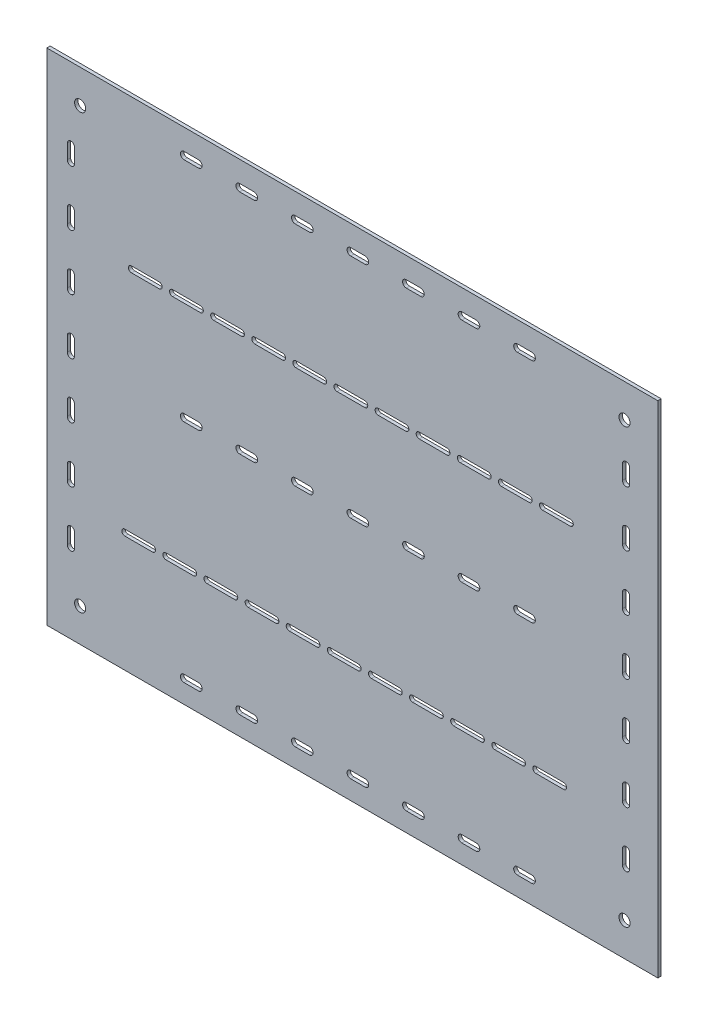
SolidWorks part; units mm, degrees
ref_plane "Alzado" through (0, 0, 0) normal (0, 0, 1) x (1, 0, 0)
ref_plane "Planta" through (0, 0, 0) normal (0, 1, 0) x (1, 0, 0)
ref_plane "Vista lateral" through (0, 0, 0) normal (1, 0, 0) x (0, 0, -1)
ref_plane "Plano1" through (0, 0, 0) normal (0, 0, -1) x (-1, 0, 0)
sketch "Croquis1" plane through (0, 0, 0) normal (0, 0, -1) x (-1, 0, 0)
  line L0 (250.0961, 147) -> (250.0961, 160)
  line L1 (256.5961, 160) -> (256.5961, 147)
  line L2 (19.8171, -120.3914) -> (-5.1829, -120.3914)
  line L3 (-5.1829, -114.9914) -> (19.8171, -114.9914)
  line L4 (-128.1829, -120.3914) -> (-153.1829, -120.3914)
  line L5 (-153.1829, -114.9914) -> (-128.1829, -114.9914)
  line L6 (93.8171, -120.3914) -> (68.8171, -120.3914)
  line L7 (68.8171, -114.9914) -> (93.8171, -114.9914)
  line L8 (-17.1829, -120.3914) -> (-42.1829, -120.3914)
  line L9 (-42.1829, -114.9914) -> (-17.1829, -114.9914)
  line L10 (167.8171, -120.3914) -> (142.8171, -120.3914)
  line L11 (142.8171, -114.9914) -> (167.8171, -114.9914)
  line L12 (56.8171, -120.3914) -> (31.8171, -120.3914)
  line L13 (31.8171, -114.9914) -> (56.8171, -114.9914)
  line L14 (179.8171, -114.9914) -> (204.8171, -114.9914)
  line L15 (204.8171, -120.3914) -> (179.8171, -120.3914)
  line L16 (105.8171, -114.9914) -> (130.8171, -114.9914)
  line L17 (130.8171, -120.3914) -> (105.8171, -120.3914)
  line L18 (-171.1819, 87.8055) -> (-196.1819, 87.8055)
  line L19 (-196.1819, 93.2055) -> (-171.1819, 93.2055)
  line L20 (-60.1819, 87.8055) -> (-85.1819, 87.8055)
  line L21 (-85.1819, 93.2055) -> (-60.1819, 93.2055)
  line L22 (51.5, -4.75) -> (38.5, -4.75)
  line L23 (38.5, 1.75) -> (51.5, 1.75)
  line L24 (151.5, -4.75) -> (138.5, -4.75)
  line L25 (138.5, 1.75) -> (151.5, 1.75)
  line L26 (13.8181, 87.8055) -> (-11.1819, 87.8055)
  line L27 (-11.1819, 93.2055) -> (13.8181, 93.2055)
  line L28 (-23.1819, 87.8055) -> (-48.1819, 87.8055)
  line L29 (-48.1819, 93.2055) -> (-23.1819, 93.2055)
  line L30 (-97.1819, 87.8055) -> (-122.1819, 87.8055)
  line L31 (-122.1819, 93.2055) -> (-97.1819, 93.2055)
  line L32 (-134.1819, 87.8055) -> (-159.1819, 87.8055)
  line L33 (-159.1819, 93.2055) -> (-134.1819, 93.2055)
  line L34 (50.8181, 87.8055) -> (25.8181, 87.8055)
  line L35 (25.8181, 93.2055) -> (50.8181, 93.2055)
  line L36 (87.8181, 87.8055) -> (62.8181, 87.8055)
  line L37 (62.8181, 93.2055) -> (87.8181, 93.2055)
  line L38 (-165.1829, -120.3914) -> (-190.1829, -120.3914)
  line L39 (-190.1829, -114.9914) -> (-165.1829, -114.9914)
  line L40 (161.8181, 87.8055) -> (136.8181, 87.8055)
  line L41 (136.8181, 93.2055) -> (161.8181, 93.2055)
  line L42 (-54.1829, -120.3914) -> (-79.1829, -120.3914)
  line L43 (-79.1829, -114.9914) -> (-54.1829, -114.9914)
  line L44 (-91.1829, -120.3914) -> (-116.1829, -120.3914)
  line L45 (-116.1829, -114.9914) -> (-91.1829, -114.9914)
  line L46 (99.8181, 93.2055) -> (124.8181, 93.2055)
  line L47 (124.8181, 87.8055) -> (99.8181, 87.8055)
  line L48 (173.8181, 93.2055) -> (198.8181, 93.2055)
  line L49 (198.8181, 87.8055) -> (173.8181, 87.8055)
  line L50 (-98.5, -4.75) -> (-111.5, -4.75)
  line L51 (-111.5, 1.75) -> (-98.5, 1.75)
  line L52 (101.5, -4.75) -> (88.5, -4.75)
  line L53 (88.5, 1.75) -> (101.5, 1.75)
  line L54 (1.5, -4.75) -> (-11.5, -4.75)
  line L55 (-11.5, 1.75) -> (1.5, 1.75)
  line L56 (-48.5, -4.75) -> (-61.5, -4.75)
  line L57 (-61.5, 1.75) -> (-48.5, 1.75)
  line L58 (151.5, -207.9595) -> (138.5, -207.9595)
  line L59 (138.5, -201.4595) -> (151.5, -201.4595)
  line L60 (-148.5, -4.75) -> (-161.5, -4.75)
  line L61 (-161.5, 1.75) -> (-148.5, 1.75)
  line L62 (101.5, -207.9595) -> (88.5, -207.9595)
  line L63 (88.5, -201.4595) -> (101.5, -201.4595)
  line L64 (51.5, -207.9595) -> (38.5, -207.9595)
  line L65 (38.5, -201.4595) -> (51.5, -201.4595)
  line L66 (101.5, 199.605) -> (88.5, 199.605)
  line L67 (88.5, 206.105) -> (101.5, 206.105)
  line L68 (-98.5, 199.605) -> (-111.5, 199.605)
  line L69 (-111.5, 206.105) -> (-98.5, 206.105)
  line L70 (151.5, 199.605) -> (138.5, 199.605)
  line L71 (138.5, 206.105) -> (151.5, 206.105)
  line L72 (51.5, 199.605) -> (38.5, 199.605)
  line L73 (38.5, 206.105) -> (51.5, 206.105)
  line L74 (1.5, -207.9595) -> (-11.5, -207.9595)
  line L75 (-11.5, -201.4595) -> (1.5, -201.4595)
  line L76 (-148.5, -207.9595) -> (-161.5, -207.9595)
  line L77 (-161.5, -201.4595) -> (-148.5, -201.4595)
  line L78 (-98.5, -207.9595) -> (-111.5, -207.9595)
  line L79 (-111.5, -201.4595) -> (-98.5, -201.4595)
  line L80 (-48.5, -207.9595) -> (-61.5, -207.9595)
  line L81 (-61.5, -201.4595) -> (-48.5, -201.4595)
  line L82 (-148.5, 199.605) -> (-161.5, 199.605)
  line L83 (-161.5, 206.105) -> (-148.5, 206.105)
  line L84 (-249.6493, -153) -> (-249.6493, -140)
  line L85 (-243.1493, -140) -> (-243.1493, -153)
  line L86 (-48.5, 199.605) -> (-61.5, 199.605)
  line L87 (-61.5, 206.105) -> (-48.5, 206.105)
  line L88 (1.5, 199.605) -> (-11.5, 199.605)
  line L89 (-11.5, 206.105) -> (1.5, 206.105)
  line L90 (-249.6493, 97) -> (-249.6493, 110)
  line L91 (-243.1493, 110) -> (-243.1493, 97)
  line L92 (-249.6493, 47) -> (-249.6493, 60)
  line L93 (-243.1493, 60) -> (-243.1493, 47)
  line L94 (-249.6493, -53) -> (-249.6493, -40)
  line L95 (-243.1493, -40) -> (-243.1493, -53)
  line L96 (-249.6493, -103) -> (-249.6493, -90)
  line L97 (-243.1493, -90) -> (-243.1493, -103)
  line L98 (250.0961, -153) -> (250.0961, -140)
  line L99 (256.5961, -140) -> (256.5961, -153)
  line L100 (250.0961, -53) -> (250.0961, -40)
  line L101 (256.5961, -40) -> (256.5961, -53)
  line L102 (-249.6493, -3) -> (-249.6493, 10)
  line L103 (-243.1493, 10) -> (-243.1493, -3)
  line L104 (-249.6493, 147) -> (-249.6493, 160)
  line L105 (-243.1493, 160) -> (-243.1493, 147)
  line L106 (250.0961, 97) -> (250.0961, 110)
  line L107 (256.5961, 110) -> (256.5961, 97)
  line L108 (250.0961, -103) -> (250.0961, -90)
  line L109 (256.5961, -90) -> (256.5961, -103)
  line L110 (250.0961, -3) -> (250.0961, 10)
  line L111 (256.5961, 10) -> (256.5961, -3)
  line L112 (250.0961, 47) -> (250.0961, 60)
  line L113 (256.5961, 60) -> (256.5961, 47)
  line L114 (-275, 225) -> (-275, -225)
  line L115 (-275, -225) -> (275, -225)
  line L116 (275, -225) -> (275, 225)
  line L117 (275, 225) -> (-275, 225)
  circle A0 centre (-245, -195) radius 5
  circle A1 centre (245, -195) radius 5
  circle A2 centre (-245, 195) radius 5
  circle A3 centre (245, 195) radius 5
  arc A4 (250.0961, 160) -> (256.5961, 160) centre (253.3461, 160) cw
  arc A5 (256.5961, 147) -> (250.0961, 147) centre (253.3461, 147) cw
  arc A6 (-5.1829, -120.3914) -> (-5.1829, -114.9914) centre (-5.1829, -117.6914) cw
  arc A7 (19.8171, -114.9914) -> (19.8171, -120.3914) centre (19.8171, -117.6914) cw
  arc A8 (-153.1829, -120.3914) -> (-153.1829, -114.9914) centre (-153.1829, -117.6914) cw
  arc A9 (-128.1829, -114.9914) -> (-128.1829, -120.3914) centre (-128.1829, -117.6914) cw
  arc A10 (68.8171, -120.3914) -> (68.8171, -114.9914) centre (68.8171, -117.6914) cw
  arc A11 (93.8171, -114.9914) -> (93.8171, -120.3914) centre (93.8171, -117.6914) cw
  arc A12 (-42.1829, -120.3914) -> (-42.1829, -114.9914) centre (-42.1829, -117.6914) cw
  arc A13 (-17.1829, -114.9914) -> (-17.1829, -120.3914) centre (-17.1829, -117.6914) cw
  arc A14 (142.8171, -120.3914) -> (142.8171, -114.9914) centre (142.8171, -117.6914) cw
  arc A15 (167.8171, -114.9914) -> (167.8171, -120.3914) centre (167.8171, -117.6914) cw
  arc A16 (31.8171, -120.3914) -> (31.8171, -114.9914) centre (31.8171, -117.6914) cw
  arc A17 (56.8171, -114.9914) -> (56.8171, -120.3914) centre (56.8171, -117.6914) cw
  arc A18 (204.8171, -114.9914) -> (204.8171, -120.3914) centre (204.8171, -117.6914) cw
  arc A19 (179.8171, -120.3914) -> (179.8171, -114.9914) centre (179.8171, -117.6914) cw
  arc A20 (130.8171, -114.9914) -> (130.8171, -120.3914) centre (130.8171, -117.6914) cw
  arc A21 (105.8171, -120.3914) -> (105.8171, -114.9914) centre (105.8171, -117.6914) cw
  arc A22 (-196.1819, 87.8055) -> (-196.1819, 93.2055) centre (-196.1819, 90.5055) cw
  arc A23 (-171.1819, 93.2055) -> (-171.1819, 87.8055) centre (-171.1819, 90.5055) cw
  arc A24 (-85.1819, 87.8055) -> (-85.1819, 93.2055) centre (-85.1819, 90.5055) cw
  arc A25 (-60.1819, 93.2055) -> (-60.1819, 87.8055) centre (-60.1819, 90.5055) cw
  arc A26 (38.5, -4.75) -> (38.5, 1.75) centre (38.5, -1.5) cw
  arc A27 (51.5, 1.75) -> (51.5, -4.75) centre (51.5, -1.5) cw
  arc A28 (138.5, -4.75) -> (138.5, 1.75) centre (138.5, -1.5) cw
  arc A29 (151.5, 1.75) -> (151.5, -4.75) centre (151.5, -1.5) cw
  arc A30 (-11.1819, 87.8055) -> (-11.1819, 93.2055) centre (-11.1819, 90.5055) cw
  arc A31 (13.8181, 93.2055) -> (13.8181, 87.8055) centre (13.8181, 90.5055) cw
  arc A32 (-48.1819, 87.8055) -> (-48.1819, 93.2055) centre (-48.1819, 90.5055) cw
  arc A33 (-23.1819, 93.2055) -> (-23.1819, 87.8055) centre (-23.1819, 90.5055) cw
  arc A34 (-122.1819, 87.8055) -> (-122.1819, 93.2055) centre (-122.1819, 90.5055) cw
  arc A35 (-97.1819, 93.2055) -> (-97.1819, 87.8055) centre (-97.1819, 90.5055) cw
  arc A36 (-159.1819, 87.8055) -> (-159.1819, 93.2055) centre (-159.1819, 90.5055) cw
  arc A37 (-134.1819, 93.2055) -> (-134.1819, 87.8055) centre (-134.1819, 90.5055) cw
  arc A38 (25.8181, 87.8055) -> (25.8181, 93.2055) centre (25.8181, 90.5055) cw
  arc A39 (50.8181, 93.2055) -> (50.8181, 87.8055) centre (50.8181, 90.5055) cw
  arc A40 (62.8181, 87.8055) -> (62.8181, 93.2055) centre (62.8181, 90.5055) cw
  arc A41 (87.8181, 93.2055) -> (87.8181, 87.8055) centre (87.8181, 90.5055) cw
  arc A42 (-190.1829, -120.3914) -> (-190.1829, -114.9914) centre (-190.1829, -117.6914) cw
  arc A43 (-165.1829, -114.9914) -> (-165.1829, -120.3914) centre (-165.1829, -117.6914) cw
  arc A44 (136.8181, 87.8055) -> (136.8181, 93.2055) centre (136.8181, 90.5055) cw
  arc A45 (161.8181, 93.2055) -> (161.8181, 87.8055) centre (161.8181, 90.5055) cw
  arc A46 (-79.1829, -120.3914) -> (-79.1829, -114.9914) centre (-79.1829, -117.6914) cw
  arc A47 (-54.1829, -114.9914) -> (-54.1829, -120.3914) centre (-54.1829, -117.6914) cw
  arc A48 (-116.1829, -120.3914) -> (-116.1829, -114.9914) centre (-116.1829, -117.6914) cw
  arc A49 (-91.1829, -114.9914) -> (-91.1829, -120.3914) centre (-91.1829, -117.6914) cw
  arc A50 (124.8181, 93.2055) -> (124.8181, 87.8055) centre (124.8181, 90.5055) cw
  arc A51 (99.8181, 87.8055) -> (99.8181, 93.2055) centre (99.8181, 90.5055) cw
  arc A52 (198.8181, 93.2055) -> (198.8181, 87.8055) centre (198.8181, 90.5055) cw
  arc A53 (173.8181, 87.8055) -> (173.8181, 93.2055) centre (173.8181, 90.5055) cw
  arc A54 (-111.5, -4.75) -> (-111.5, 1.75) centre (-111.5, -1.5) cw
  arc A55 (-98.5, 1.75) -> (-98.5, -4.75) centre (-98.5, -1.5) cw
  arc A56 (88.5, -4.75) -> (88.5, 1.75) centre (88.5, -1.5) cw
  arc A57 (101.5, 1.75) -> (101.5, -4.75) centre (101.5, -1.5) cw
  arc A58 (-11.5, -4.75) -> (-11.5, 1.75) centre (-11.5, -1.5) cw
  arc A59 (1.5, 1.75) -> (1.5, -4.75) centre (1.5, -1.5) cw
  arc A60 (-61.5, -4.75) -> (-61.5, 1.75) centre (-61.5, -1.5) cw
  arc A61 (-48.5, 1.75) -> (-48.5, -4.75) centre (-48.5, -1.5) cw
  arc A62 (138.5, -207.9595) -> (138.5, -201.4595) centre (138.5, -204.7095) cw
  arc A63 (151.5, -201.4595) -> (151.5, -207.9595) centre (151.5, -204.7095) cw
  arc A64 (-161.5, -4.75) -> (-161.5, 1.75) centre (-161.5, -1.5) cw
  arc A65 (-148.5, 1.75) -> (-148.5, -4.75) centre (-148.5, -1.5) cw
  arc A66 (88.5, -207.9595) -> (88.5, -201.4595) centre (88.5, -204.7095) cw
  arc A67 (101.5, -201.4595) -> (101.5, -207.9595) centre (101.5, -204.7095) cw
  arc A68 (38.5, -207.9595) -> (38.5, -201.4595) centre (38.5, -204.7095) cw
  arc A69 (51.5, -201.4595) -> (51.5, -207.9595) centre (51.5, -204.7095) cw
  arc A70 (88.5, 199.605) -> (88.5, 206.105) centre (88.5, 202.855) cw
  arc A71 (101.5, 206.105) -> (101.5, 199.605) centre (101.5, 202.855) cw
  arc A72 (-111.5, 199.605) -> (-111.5, 206.105) centre (-111.5, 202.855) cw
  arc A73 (-98.5, 206.105) -> (-98.5, 199.605) centre (-98.5, 202.855) cw
  arc A74 (138.5, 199.605) -> (138.5, 206.105) centre (138.5, 202.855) cw
  arc A75 (151.5, 206.105) -> (151.5, 199.605) centre (151.5, 202.855) cw
  arc A76 (38.5, 199.605) -> (38.5, 206.105) centre (38.5, 202.855) cw
  arc A77 (51.5, 206.105) -> (51.5, 199.605) centre (51.5, 202.855) cw
  arc A78 (-11.5, -207.9595) -> (-11.5, -201.4595) centre (-11.5, -204.7095) cw
  arc A79 (1.5, -201.4595) -> (1.5, -207.9595) centre (1.5, -204.7095) cw
  arc A80 (-161.5, -207.9595) -> (-161.5, -201.4595) centre (-161.5, -204.7095) cw
  arc A81 (-148.5, -201.4595) -> (-148.5, -207.9595) centre (-148.5, -204.7095) cw
  arc A82 (-111.5, -207.9595) -> (-111.5, -201.4595) centre (-111.5, -204.7095) cw
  arc A83 (-98.5, -201.4595) -> (-98.5, -207.9595) centre (-98.5, -204.7095) cw
  arc A84 (-61.5, -207.9595) -> (-61.5, -201.4595) centre (-61.5, -204.7095) cw
  arc A85 (-48.5, -201.4595) -> (-48.5, -207.9595) centre (-48.5, -204.7095) cw
  arc A86 (-161.5, 199.605) -> (-161.5, 206.105) centre (-161.5, 202.855) cw
  arc A87 (-148.5, 206.105) -> (-148.5, 199.605) centre (-148.5, 202.855) cw
  arc A88 (-249.6493, -140) -> (-243.1493, -140) centre (-246.3993, -140) cw
  arc A89 (-243.1493, -153) -> (-249.6493, -153) centre (-246.3993, -153) cw
  arc A90 (-61.5, 199.605) -> (-61.5, 206.105) centre (-61.5, 202.855) cw
  arc A91 (-48.5, 206.105) -> (-48.5, 199.605) centre (-48.5, 202.855) cw
  arc A92 (-11.5, 199.605) -> (-11.5, 206.105) centre (-11.5, 202.855) cw
  arc A93 (1.5, 206.105) -> (1.5, 199.605) centre (1.5, 202.855) cw
  arc A94 (-249.6493, 110) -> (-243.1493, 110) centre (-246.3993, 110) cw
  arc A95 (-243.1493, 97) -> (-249.6493, 97) centre (-246.3993, 97) cw
  arc A96 (-249.6493, 60) -> (-243.1493, 60) centre (-246.3993, 60) cw
  arc A97 (-243.1493, 47) -> (-249.6493, 47) centre (-246.3993, 47) cw
  arc A98 (-249.6493, -40) -> (-243.1493, -40) centre (-246.3993, -40) cw
  arc A99 (-243.1493, -53) -> (-249.6493, -53) centre (-246.3993, -53) cw
  arc A100 (-249.6493, -90) -> (-243.1493, -90) centre (-246.3993, -90) cw
  arc A101 (-243.1493, -103) -> (-249.6493, -103) centre (-246.3993, -103) cw
  arc A102 (250.0961, -140) -> (256.5961, -140) centre (253.3461, -140) cw
  arc A103 (256.5961, -153) -> (250.0961, -153) centre (253.3461, -153) cw
  arc A104 (250.0961, -40) -> (256.5961, -40) centre (253.3461, -40) cw
  arc A105 (256.5961, -53) -> (250.0961, -53) centre (253.3461, -53) cw
  arc A106 (-249.6493, 10) -> (-243.1493, 10) centre (-246.3993, 10) cw
  arc A107 (-243.1493, -3) -> (-249.6493, -3) centre (-246.3993, -3) cw
  arc A108 (-249.6493, 160) -> (-243.1493, 160) centre (-246.3993, 160) cw
  arc A109 (-243.1493, 147) -> (-249.6493, 147) centre (-246.3993, 147) cw
  arc A110 (250.0961, 110) -> (256.5961, 110) centre (253.3461, 110) cw
  arc A111 (256.5961, 97) -> (250.0961, 97) centre (253.3461, 97) cw
  arc A112 (250.0961, -90) -> (256.5961, -90) centre (253.3461, -90) cw
  arc A113 (256.5961, -103) -> (250.0961, -103) centre (253.3461, -103) cw
  arc A114 (250.0961, 10) -> (256.5961, 10) centre (253.3461, 10) cw
  arc A115 (256.5961, -3) -> (250.0961, -3) centre (253.3461, -3) cw
  arc A116 (250.0961, 60) -> (256.5961, 60) centre (253.3461, 60) cw
  arc A117 (256.5961, 47) -> (250.0961, 47) centre (253.3461, 47) cw
extrude "Saliente-Extruir1" add sketch "Croquis1" against normal blind 3
